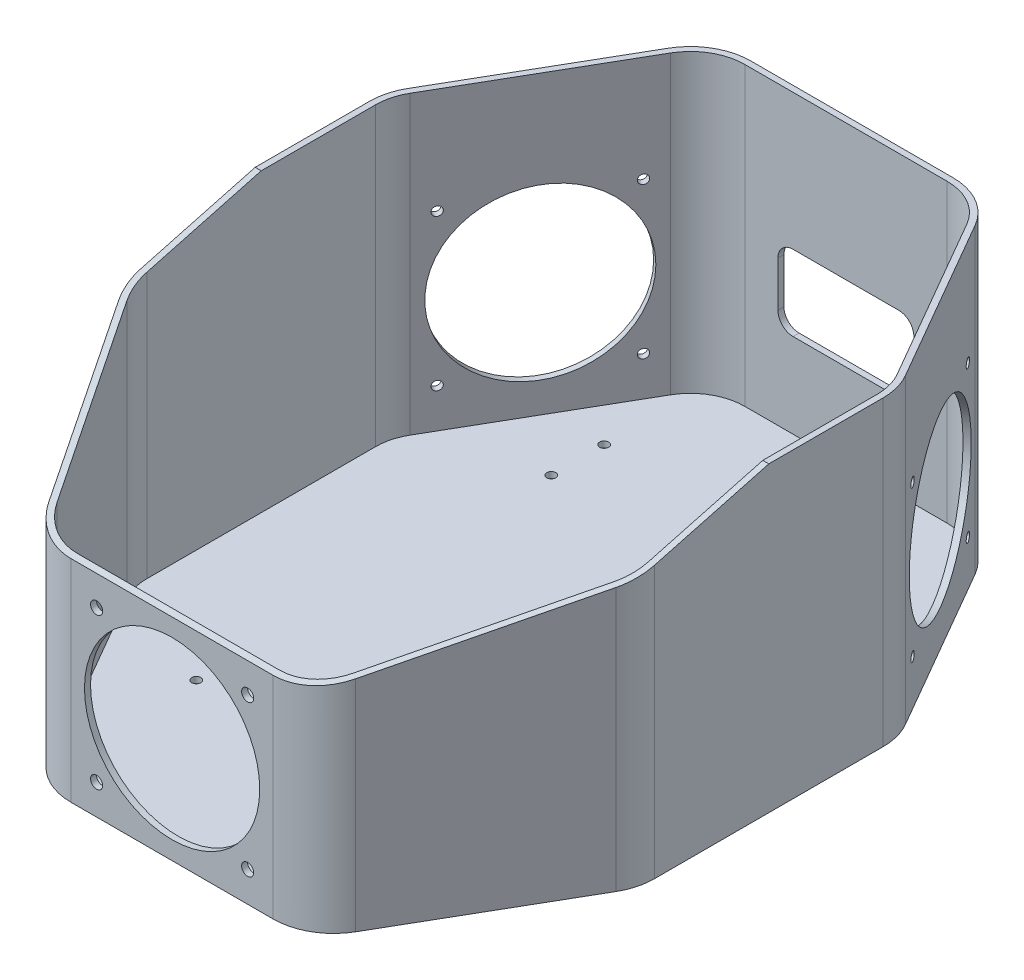
SolidWorks part; units mm, degrees
ref_plane "Alzado" through (0, 0, 0) normal (0, 0, 1) x (1, 0, 0)
ref_plane "Planta" through (0, 0, 0) normal (0, 1, 0) x (1, 0, 0)
ref_plane "Vista lateral" through (0, 0, 0) normal (1, 0, 0) x (0, 0, -1)
sketch "Croquis1" plane through (0, 0, 0) normal (0, 1, 0) x (1, 0, 0)
  line L0 (-82.3205, 47.859) -> (-50.7735, 102.5)
  line L1 (-33.453, 112.5) -> (33.453, 112.5)
  line L2 (-85, 37.859) -> (-85, -37.859)
  line L3 (-65, -112.5) -> (65, -112.5) construction
  line L4 (85, 37.859) -> (85, -37.859)
  line L5 (-85, 112.5) -> (85, -112.5) construction
  line L6 (-85, -112.5) -> (85, 112.5) construction
  line L7 (0, 0) -> (0, 35.0425) construction
  line L8 (82.3205, 47.859) -> (50.7735, 102.5)
  line L9 (-85, 112.5) -> (-45, 112.5) construction
  line L10 (0, 0) -> (34.8014, 0) construction
  line L11 (82.3205, -47.859) -> (50.7735, -102.5)
  line L12 (-33.453, -112.5) -> (33.453, -112.5)
  line L13 (-82.3205, -47.859) -> (-50.7735, -102.5)
  arc A0 (-85, -92.5) -> (-65, -112.5) centre (-65, -92.5) ccw construction
  arc A1 (65, -112.5) -> (85, -92.5) centre (65, -92.5) ccw construction
  arc A2 (82.3205, 47.859) -> (85, 37.859) centre (65, 37.859) cw
  arc A3 (50.7735, 102.5) -> (33.453, 112.5) centre (33.453, 92.5) ccw
  arc A4 (-50.7735, 102.5) -> (-33.453, 112.5) centre (-33.453, 92.5) cw
  arc A5 (-82.3205, 47.859) -> (-85, 37.859) centre (-65, 37.859) ccw
  arc A6 (82.3205, -47.859) -> (85, -37.859) centre (65, -37.859) ccw
  arc A7 (50.7735, -102.5) -> (33.453, -112.5) centre (33.453, -92.5) cw
  arc A8 (-50.7735, -102.5) -> (-33.453, -112.5) centre (-33.453, -92.5) ccw
  arc A9 (-82.3205, -47.859) -> (-85, -37.859) centre (-65, -37.859) cw
  point P0 (0, 0)
  point P21 (85, 43.218)
  point P24 (45, 112.5)
  point P30 (-85, 43.218)
  dimension "D5" = 20
  dimension "D1" = 30
  dimension "D2" = 80
  dimension "D3" = 225
  dimension "D4" = 170
extrude "Saliente-Extruir1" add sketch "Croquis1" along normal blind 100
shell "Vaciado2" thickness 2
sketch "Croquis2" plane through (0, 0, 0) normal (0, 1, 0) x (1, 0, 0)
  line L0 (0, 58.75) -> (0, -58.75) construction
  line L1 (-45.75, 58.75) -> (45.75, 58.75) construction
  line L2 (-45.75, -58.75) -> (45.75, -58.75) construction
  line L3 (-45.75, 58.75) -> (-45.75, 76.25) construction
  line L4 (45.75, -58.75) -> (45.75, -76.25) construction
  line L5 (-45.75, 76.25) -> (-40.1485, 76.25) construction
  line L6 (83, -37.859) -> (83, 37.859)
  line L7 (80.5885, 46.859) -> (49.0415, 101.5)
  line L8 (33.453, 110.5) -> (-33.453, 110.5)
  line L9 (-49.0415, 101.5) -> (-80.5885, 46.859)
  line L10 (-83, 37.859) -> (-83, -37.859)
  line L11 (-80.5885, -46.859) -> (-49.0415, -101.5)
  line L12 (83, -37.859) -> (83, 37.859) construction
  line L13 (80.5885, 46.859) -> (49.0415, 101.5) construction
  line L14 (33.453, 110.5) -> (-33.453, 110.5) construction
  line L15 (-49.0415, 101.5) -> (-80.5885, 46.859) construction
  line L16 (-83, 37.859) -> (-83, -37.859) construction
  line L18 (-35.75, 76.25) -> (25.75, 76.25) construction
  line L19 (-35.75, 76.25) -> (-35.75, 48.75) construction
  line L20 (-35.75, 48.75) -> (25.75, 48.75) construction
  line L21 (25.75, 76.25) -> (25.75, 48.75) construction
  line L22 (-35.75, 76.25) -> (25.75, 48.75) construction
  line L23 (-35.75, 48.75) -> (25.75, 76.25) construction
  line L24 (45.75, -76.25) -> (34.6741, -76.25) construction
  line L25 (-25.75, -76.25) -> (35.75, -76.25) construction
  line L26 (-25.75, -76.25) -> (-25.75, -13.75) construction
  line L27 (-25.75, -13.75) -> (35.75, -13.75) construction
  line L28 (35.75, -76.25) -> (35.75, -13.75) construction
  line L29 (-25.75, -76.25) -> (35.75, -13.75) construction
  line L30 (-25.75, -13.75) -> (35.75, -76.25) construction
  line L37 (-80.5885, -46.859) -> (-49.0415, -101.5) construction
  line L42 (-33.453, -110.5) -> (33.453, -110.5)
  line L44 (-33.453, -110.5) -> (33.453, -110.5) construction
  line L45 (49.0415, -101.5) -> (80.5885, -46.859)
  line L46 (49.0415, -101.5) -> (80.5885, -46.859) construction
  circle A0 centre (-45.75, 76.25) radius 1.5
  circle A1 centre (-45.75, 58.75) radius 1.5
  circle A2 centre (45.75, 58.75) radius 1.5
  circle A3 centre (-45.75, -58.75) radius 1.5
  circle A4 centre (45.75, -58.75) radius 1.5
  circle A5 centre (45.75, -76.25) radius 1.5
  arc A12 (-83, -37.859) -> (-80.5885, -46.859) centre (-65, -37.859) ccw
  arc A14 (-83, -37.859) -> (-80.5885, -46.859) centre (-65, -37.859) ccw construction
  arc A16 (83, 37.859) -> (80.5885, 46.859) centre (65, 37.859) ccw
  arc A17 (83, 37.859) -> (80.5885, 46.859) centre (65, 37.859) ccw construction
  arc A18 (49.0415, 101.5) -> (33.453, 110.5) centre (33.453, 92.5) ccw
  arc A19 (49.0415, 101.5) -> (33.453, 110.5) centre (33.453, 92.5) ccw construction
  arc A20 (-33.453, 110.5) -> (-49.0415, 101.5) centre (-33.453, 92.5) ccw
  arc A21 (-33.453, 110.5) -> (-49.0415, 101.5) centre (-33.453, 92.5) ccw construction
  arc A22 (-80.5885, 46.859) -> (-83, 37.859) centre (-65, 37.859) ccw
  arc A23 (-80.5885, 46.859) -> (-83, 37.859) centre (-65, 37.859) ccw construction
  arc A24 (-49.0415, -101.5) -> (-33.453, -110.5) centre (-33.453, -92.5) ccw
  arc A25 (-49.0415, -101.5) -> (-33.453, -110.5) centre (-33.453, -92.5) ccw construction
  arc A30 (33.453, -110.5) -> (49.0415, -101.5) centre (33.453, -92.5) ccw
  arc A31 (33.453, -110.5) -> (49.0415, -101.5) centre (33.453, -92.5) ccw construction
  arc A32 (80.5885, -46.859) -> (83, -37.859) centre (65, -37.859) ccw
  arc A33 (80.5885, -46.859) -> (83, -37.859) centre (65, -37.859) ccw construction
  point P21 (-5, 62.5)
  point P26 (5, -45)
  dimension "D5" = 3
  dimension "D2" = 91.5
  dimension "D3" = 17.5
  dimension "D4" = 17.5
  dimension "D6" = 10
  dimension "D7" = 20
  dimension "D8" = 10
  dimension "D9" = 20
  dimension "D10" = 10
  dimension "D11" = 45
  dimension "D12" = 117.5
  dimension "D1" = 0
extrude "Cortar-Extruir1" cut sketch "Croquis2" along normal through all both and the other way through all
sketch "Croquis3" plane through (0, 0, 0) normal (1, 0, 0) x (0, 0, -1)
  line L0 (27, 65) -> (27, 80) construction
  line L1 (-25, 65) -> (25, 65) construction
  line L2 (-25, 65) -> (-25, 15) construction
  line L3 (-25, 15) -> (25, 15) construction
  line L4 (25, 65) -> (25, 15) construction
  line L5 (-25, 65) -> (25, 15) construction
  line L6 (-25, 15) -> (25, 65) construction
  line L10 (-37.859, 0) -> (37.859, 0)
  line L11 (37.859, 0) -> (37.859, 100)
  line L12 (37.859, 100) -> (-37.859, 100)
  line L13 (-37.859, 100) -> (-37.859, 0)
  line L14 (-37.859, 0) -> (37.859, 0) construction
  line L15 (37.859, 0) -> (37.859, 100) construction
  line L16 (37.859, 100) -> (-37.859, 100) construction
  line L19 (7.5, 95.5) -> (27, 95.5) construction
  line L21 (7.5, 95.5) -> (7.5, 80) construction
  line L22 (7.5, 80) -> (27, 80) construction
  line L23 (27, 95.5) -> (27, 80) construction
  line L24 (7.5, 95.5) -> (27, 80) construction
  line L25 (7.5, 80) -> (27, 95.5) construction
  line L26 (-37.859, 100) -> (37.859, 0) construction
  line L27 (0, 40) -> (0, 50) construction
  line L30 (-37.859, 100) -> (-37.859, 0) construction
  circle A0 centre (-25, 15) radius 2
  circle A1 centre (25, 15) radius 2
  circle A2 centre (25, 65) radius 2
  circle A3 centre (-25, 65) radius 2
  circle A4 centre (0, 40) radius 29
  point P0 (0, 40)
  point P13 (17.25, 87.75)
  dimension "D6" = 4
  dimension "D10" = 58
  dimension "D1" = 50
  dimension "D2" = 50
  dimension "D4" = 15
  dimension "D7" = 19.5
  dimension "D8" = 15.5
  dimension "D9" = 15
  dimension "D3" = 0
sketch "Croquis7" plane through (0, 0, 0) normal (0, 0, 1) x (1, 0, 0)
  line L1 (25, 60) -> (-25, 60) construction
  line L2 (25, 60) -> (25, 10) construction
  line L3 (25, 10) -> (-25, 10) construction
  line L4 (-25, 60) -> (-25, 10) construction
  line L5 (25, 60) -> (-25, 10) construction
  line L6 (25, 10) -> (-25, 60) construction
  circle A0 centre (25, 60) radius 2
  circle A1 centre (-25, 60) radius 2
  circle A2 centre (-25, 10) radius 2
  circle A3 centre (25, 10) radius 2
  circle A4 centre (0, 35) radius 29
  point P0 (0, 35)
  dimension "D1" = 4
  dimension "D5" = 58
  dimension "D2" = 50
  dimension "D3" = 50
  dimension "D4" = 10
ref_plane "Plano1" through (0, 0, 0) normal (0.866, 0, -0.5) x (-0.5, 0, -0.866)
sketch "Croquis8" plane through (0, 0, 0) normal (0.866, 0, -0.5) x (-0.5, 0, -0.866)
  line L1 (6.8338, 15) -> (56.8338, 15) construction
  line L2 (6.8338, 15) -> (6.8338, 65) construction
  line L3 (6.8338, 65) -> (56.8338, 65) construction
  line L4 (0.2868, 0) -> (63.3809, 0)
  line L5 (63.3809, 0) -> (63.3809, 100)
  line L6 (63.3809, 100) -> (0.2868, 100)
  line L7 (0.2868, 100) -> (0.2868, 0)
  line L8 (0.2868, 0) -> (63.3809, 0) construction
  line L9 (63.3809, 0) -> (63.3809, 100) construction
  line L10 (63.3809, 100) -> (0.2868, 100) construction
  line L11 (0.2868, 100) -> (0.2868, 0) construction
  line L12 (56.8338, 15) -> (56.8338, 65) construction
  line L13 (6.8338, 15) -> (56.8338, 65) construction
  line L14 (6.8338, 65) -> (56.8338, 15) construction
  line L16 (31.8338, 40) -> (31.8338, 0) construction
  circle A0 centre (31.8338, 40) radius 28
  circle A1 centre (6.8338, 65) radius 1.5
  circle A2 centre (56.8338, 65) radius 1.5
  circle A3 centre (6.8338, 15) radius 1.5
  circle A4 centre (56.8338, 15) radius 1.5
  dimension "D2" = 3
  dimension "D6" = 56
  dimension "D3" = 50
  dimension "D4" = 50
  dimension "D5" = 15
  dimension "D1" = 0
extrude "Cortar-Extruir6" cut sketch "Croquis8" along normal through all
mirror "Simetría1" about plane through (0, 0, 0) normal (1, 0, 0) of "Cortar-Extruir6"
mirror "Simetría2" [suppressed] about plane through (0, 0, 0) normal (0, 0, 1)
sketch "Croquis9" plane through (0, 0, 0) normal (0, 0, 1) x (1, 0, 0)
  line L0 (0, 42.5) -> (0, 0) construction
  line L1 (33.453, 0) -> (-33.453, 0) construction
  line L2 (17.5, 55) -> (-17.5, 55)
  line L3 (22.5, 50) -> (22.5, 35)
  line L4 (17.5, 30) -> (-17.5, 30)
  line L5 (-22.5, 50) -> (-22.5, 35)
  line L6 (22.5, 55) -> (-22.5, 30) construction
  line L7 (22.5, 30) -> (-22.5, 55) construction
  arc A1 (-17.5, 55) -> (-22.5, 50) centre (-17.5, 50) ccw
  arc A2 (-17.5, 30) -> (-22.5, 35) centre (-17.5, 35) cw
  arc A3 (22.5, 35) -> (17.5, 30) centre (17.5, 35) cw
  arc A4 (17.5, 55) -> (22.5, 50) centre (17.5, 50) cw
  dimension "D1" = 5
  dimension "D2" = 30
  dimension "D3" = 25
  dimension "D4" = 45
extrude "Cortar-Extruir7" cut sketch "Croquis9" against normal through all
sketch "Croquis10" plane through (0, 0, 0) normal (1, 0, 0) x (0, 0, -1)
  line L0 (0, 0) -> (0, 100) construction
  line L1 (-37.859, 100) -> (37.859, 100) construction
  line L2 (0, 100) -> (-148.8276, 60.1218)
  line L3 (-102.5, 100) -> (-47.859, 100) construction
  line L4 (-148.8276, 60.1218) -> (-148.8276, 114.2872)
  line L5 (-148.8276, 114.2872) -> (0, 114.2872)
  line L6 (0, 114.2872) -> (0, 100)
  dimension "D1" = 15
extrude "Cortar-Extruir8" cut sketch "Croquis10" against normal through all both and the other way through all
sketch "Croquis11" plane through (0, 0, 0) normal (0, 0, 1) x (1, 0, 0)
  circle A1 centre (0, 35) radius 29
  circle A2 centre (0, 35) radius 29
  circle A3 centre (25, 10) radius 2
  circle A4 centre (25, 10) radius 2
  circle A5 centre (-25, 10) radius 2
  circle A6 centre (-25, 10) radius 2
  circle A7 centre (-25, 60) radius 2
  circle A8 centre (-25, 60) radius 2
  circle A9 centre (25, 60) radius 2
  circle A10 centre (25, 60) radius 2
  dimension "D1" = 0
  dimension "D2" = 0
  dimension "D3" = 0
  dimension "D4" = 0
  dimension "D5" = 0
extrude "Cortar-Extruir9" cut sketch "Croquis11" along normal through all
